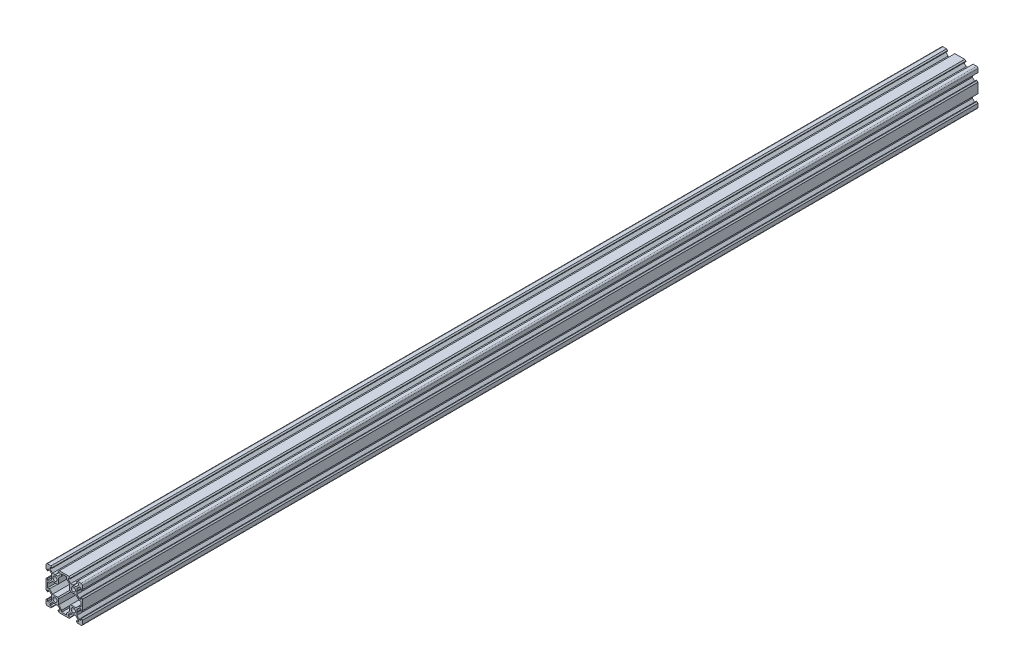
SolidWorks part; units mm, degrees
material "6061-T6 (SS)"
ref_plane "Front Plane" through (0, 0, 0) normal (0, 0, 1) x (1, 0, 0)
ref_plane "Top Plane" through (0, 0, 0) normal (0, 1, 0) x (1, 0, 0)
ref_plane "Right Plane" through (0, 0, 0) normal (1, 0, 0) x (0, 0, -1)
sketch "Sketch1" plane through (0, 0, 0) normal (0, 0, 1) x (1, 0, 0)
  line L1 (18.5, -20) -> (-18.5, -20)
  line L2 (20, -18.5) -> (20, 18.5)
  line L3 (18.5, 20) -> (-18.5, 20)
  line L4 (-20, -18.5) -> (-20, 18.5)
  line L5 (20, -20) -> (-20, 20) construction
  line L6 (20, 20) -> (-20, -20) construction
  circle A0 centre (-10, 10) radius 2.3
  circle A1 centre (10, -10) radius 2.3
  circle A2 centre (10, 10) radius 2.3
  circle A3 centre (-10, -10) radius 2.3
  arc A4 (-18.5, -20) -> (-20, -18.5) centre (-18.5, -18.5) cw
  arc A5 (18.5, -20) -> (20, -18.5) centre (18.5, -18.5) ccw
  arc A6 (20, 18.5) -> (18.5, 20) centre (18.5, 18.5) ccw
  arc A7 (-18.5, 20) -> (-20, 18.5) centre (-18.5, 18.5) ccw
  point P0 (0, 0)
  line B0 (-10, 10) -> (-10, 20) construction
  line B1 (-10, 13.69) -> (-10.21, 13.9)
  line B2 (-10.21, 13.9) -> (-12.8393, 13.9)
  line B3 (-12.8393, 13.9) -> (-15.5, 16.5607)
  line B4 (-15.5, 16.5607) -> (-15.5, 18.2)
  line B5 (-15.5, 18.2) -> (-13.395, 18.2)
  line B6 (-13.395, 18.2) -> (-13.395, 18.815)
  line B7 (-13.395, 18.815) -> (-14.58, 20)
  line B8 (-14.58, 20) -> (-5.42, 20)
  line B9 (-10, 10) -> (-15.9132, 15.9132) construction
  line B10 (-6.605, 18.815) -> (-5.42, 20)
  line B11 (-6.605, 18.2) -> (-6.605, 18.815)
  line B12 (-4.5, 18.2) -> (-6.605, 18.2)
  line B13 (-4.5, 16.5607) -> (-4.5, 18.2)
  line B14 (-7.1607, 13.9) -> (-4.5, 16.5607)
  line B15 (-9.79, 13.9) -> (-7.1607, 13.9)
  line B16 (-10, 13.69) -> (-9.79, 13.9)
  line B17 (10, 10) -> (10, 20) construction
  line B18 (10, 13.69) -> (9.79, 13.9)
  line B19 (9.79, 13.9) -> (7.1607, 13.9)
  line B20 (7.1607, 13.9) -> (4.5, 16.5607)
  line B21 (4.5, 16.5607) -> (4.5, 18.2)
  line B22 (4.5, 18.2) -> (6.605, 18.2)
  line B23 (6.605, 18.2) -> (6.605, 18.815)
  line B24 (6.605, 18.815) -> (5.42, 20)
  line B25 (5.42, 20) -> (14.58, 20)
  line B26 (10, 10) -> (4.0868, 15.9132) construction
  line B27 (13.395, 18.815) -> (14.58, 20)
  line B28 (13.395, 18.2) -> (13.395, 18.815)
  line B29 (15.5, 18.2) -> (13.395, 18.2)
  line B30 (15.5, 16.5607) -> (15.5, 18.2)
  line B31 (12.8393, 13.9) -> (15.5, 16.5607)
  line B32 (10.21, 13.9) -> (12.8393, 13.9)
  line B33 (10, 13.69) -> (10.21, 13.9)
  line B34 (-10, 10) -> (-20, 10) construction
  line B35 (-13.69, 10) -> (-13.9, 9.79)
  line B36 (-13.9, 9.79) -> (-13.9, 7.1607)
  line B37 (-13.9, 7.1607) -> (-16.5607, 4.5)
  line B38 (-16.5607, 4.5) -> (-18.2, 4.5)
  line B39 (-18.2, 4.5) -> (-18.2, 6.605)
  line B40 (-18.2, 6.605) -> (-18.815, 6.605)
  line B41 (-18.815, 6.605) -> (-20, 5.42)
  line B42 (-20, 5.42) -> (-20, 14.58)
  line B43 (-10, 10) -> (-15.9132, 4.0868) construction
  line B44 (-18.815, 13.395) -> (-20, 14.58)
  line B45 (-18.2, 13.395) -> (-18.815, 13.395)
  line B46 (-18.2, 15.5) -> (-18.2, 13.395)
  line B47 (-16.5607, 15.5) -> (-18.2, 15.5)
  line B48 (-13.9, 12.8393) -> (-16.5607, 15.5)
  line B49 (-13.9, 10.21) -> (-13.9, 12.8393)
  line B50 (-13.69, 10) -> (-13.9, 10.21)
  line B51 (-10, -10) -> (-20, -10) construction
  line B52 (-13.69, -10) -> (-13.9, -10.21)
  line B53 (-13.9, -10.21) -> (-13.9, -12.8393)
  line B54 (-13.9, -12.8393) -> (-16.5607, -15.5)
  line B55 (-16.5607, -15.5) -> (-18.2, -15.5)
  line B56 (-18.2, -15.5) -> (-18.2, -13.395)
  line B57 (-18.2, -13.395) -> (-18.815, -13.395)
  line B58 (-18.815, -13.395) -> (-20, -14.58)
  line B59 (-20, -14.58) -> (-20, -5.42)
  line B60 (-10, -10) -> (-15.9132, -15.9132) construction
  line B61 (-18.815, -6.605) -> (-20, -5.42)
  line B62 (-18.2, -6.605) -> (-18.815, -6.605)
  line B63 (-18.2, -4.5) -> (-18.2, -6.605)
  line B64 (-16.5607, -4.5) -> (-18.2, -4.5)
  line B65 (-13.9, -7.1607) -> (-16.5607, -4.5)
  line B66 (-13.9, -9.79) -> (-13.9, -7.1607)
  line B67 (-13.69, -10) -> (-13.9, -9.79)
  line B68 (-10, -10) -> (-10, -20) construction
  line B69 (-10, -13.69) -> (-9.79, -13.9)
  line B70 (-9.79, -13.9) -> (-7.1607, -13.9)
  line B71 (-7.1607, -13.9) -> (-4.5, -16.5607)
  line B72 (-4.5, -16.5607) -> (-4.5, -18.2)
  line B73 (-4.5, -18.2) -> (-6.605, -18.2)
  line B74 (-6.605, -18.2) -> (-6.605, -18.815)
  line B75 (-6.605, -18.815) -> (-5.42, -20)
  line B76 (-5.42, -20) -> (-14.58, -20)
  line B77 (-10, -10) -> (-4.0868, -15.9132) construction
  line B78 (-13.395, -18.815) -> (-14.58, -20)
  line B79 (-13.395, -18.2) -> (-13.395, -18.815)
  line B80 (-15.5, -18.2) -> (-13.395, -18.2)
  line B81 (-15.5, -16.5607) -> (-15.5, -18.2)
  line B82 (-12.8393, -13.9) -> (-15.5, -16.5607)
  line B83 (-10.21, -13.9) -> (-12.8393, -13.9)
  line B84 (-10, -13.69) -> (-10.21, -13.9)
  line B85 (10, -10) -> (10, -20) construction
  line B86 (10, -13.69) -> (10.21, -13.9)
  line B87 (10.21, -13.9) -> (12.8393, -13.9)
  line B88 (12.8393, -13.9) -> (15.5, -16.5607)
  line B89 (15.5, -16.5607) -> (15.5, -18.2)
  line B90 (15.5, -18.2) -> (13.395, -18.2)
  line B91 (13.395, -18.2) -> (13.395, -18.815)
  line B92 (13.395, -18.815) -> (14.58, -20)
  line B93 (14.58, -20) -> (5.42, -20)
  line B94 (10, -10) -> (15.9132, -15.9132) construction
  line B95 (6.605, -18.815) -> (5.42, -20)
  line B96 (6.605, -18.2) -> (6.605, -18.815)
  line B97 (4.5, -18.2) -> (6.605, -18.2)
  line B98 (4.5, -16.5607) -> (4.5, -18.2)
  line B99 (7.1607, -13.9) -> (4.5, -16.5607)
  line B100 (9.79, -13.9) -> (7.1607, -13.9)
  line B101 (10, -13.69) -> (9.79, -13.9)
  line B102 (10, 10) -> (20, 10) construction
  line B103 (13.69, 10) -> (13.9, 10.21)
  line B104 (13.9, 10.21) -> (13.9, 12.8393)
  line B105 (13.9, 12.8393) -> (16.5607, 15.5)
  line B106 (16.5607, 15.5) -> (18.2, 15.5)
  line B107 (18.2, 15.5) -> (18.2, 13.395)
  line B108 (18.2, 13.395) -> (18.815, 13.395)
  line B109 (18.815, 13.395) -> (20, 14.58)
  line B110 (20, 14.58) -> (20, 5.42)
  line B111 (10, 10) -> (15.9132, 15.9132) construction
  line B112 (18.815, 6.605) -> (20, 5.42)
  line B113 (18.2, 6.605) -> (18.815, 6.605)
  line B114 (18.2, 4.5) -> (18.2, 6.605)
  line B115 (16.5607, 4.5) -> (18.2, 4.5)
  line B116 (13.9, 7.1607) -> (16.5607, 4.5)
  line B117 (13.9, 9.79) -> (13.9, 7.1607)
  line B118 (13.69, 10) -> (13.9, 9.79)
  line B119 (10, -10) -> (20, -10) construction
  line B120 (13.69, -10) -> (13.9, -9.79)
  line B121 (13.9, -9.79) -> (13.9, -7.1607)
  line B122 (13.9, -7.1607) -> (16.5607, -4.5)
  line B123 (16.5607, -4.5) -> (18.2, -4.5)
  line B124 (18.2, -4.5) -> (18.2, -6.605)
  line B125 (18.2, -6.605) -> (18.815, -6.605)
  line B126 (18.815, -6.605) -> (20, -5.42)
  line B127 (20, -5.42) -> (20, -14.58)
  line B128 (10, -10) -> (15.9132, -4.0868) construction
  line B129 (18.815, -13.395) -> (20, -14.58)
  line B130 (18.2, -13.395) -> (18.815, -13.395)
  line B131 (18.2, -15.5) -> (18.2, -13.395)
  line B132 (16.5607, -15.5) -> (18.2, -15.5)
  line B133 (13.9, -12.8393) -> (16.5607, -15.5)
  line B134 (13.9, -10.21) -> (13.9, -12.8393)
  line B135 (13.69, -10) -> (13.9, -10.21)
  line B136 (-18.2, -2.7) -> (-18.2, 2.7)
  line B137 (-18.2, 2.7) -> (-16.2393, 2.7)
  line B138 (-16.2393, 2.7) -> (-12.8393, 6.1)
  line B139 (-12.8393, 6.1) -> (-7.1607, 6.1)
  line B140 (-10, 6.1) -> (-10, 0) construction
  line B141 (-10, 0) -> (-18.2, 0) construction
  line B142 (-12.8393, -6.1) -> (-7.1607, -6.1)
  line B143 (-16.2393, -2.7) -> (-12.8393, -6.1)
  line B144 (-18.2, -2.7) -> (-16.2393, -2.7)
  line B145 (-10, 6.1) -> (-10, 10) construction
  line B146 (-10, 10) -> (-15.0927, 4.9073) construction
  line B147 (-10, 10) -> (-6.3747, 6.3747) construction
  line B148 (2.7, 18.2) -> (2.7, 16.2393)
  line B149 (2.7, 16.2393) -> (6.1, 12.8393)
  line B150 (6.1, 12.8393) -> (6.1, 7.1607)
  line B151 (-6.1, 12.8393) -> (-6.1, 7.1607)
  line B152 (-2.7, 16.2393) -> (-6.1, 12.8393)
  line B153 (-2.7, 18.2) -> (-2.7, 16.2393)
  line B154 (2.7, 18.2) -> (-2.7, 18.2)
  line B155 (2.7, -18.2) -> (-2.7, -18.2)
  line B156 (-2.7, -18.2) -> (-2.7, -16.2393)
  line B157 (-2.7, -16.2393) -> (-6.1, -12.8393)
  line B158 (-6.1, -12.8393) -> (-6.1, -7.1607)
  line B159 (6.1, -12.8393) -> (6.1, -7.1607)
  line B160 (2.7, -16.2393) -> (6.1, -12.8393)
  line B161 (2.7, -18.2) -> (2.7, -16.2393)
  line B162 (0, 18.2) -> (0, -18.2) construction
  line B163 (12.8393, -6.1) -> (7.1607, -6.1)
  line B164 (16.2393, -2.7) -> (12.8393, -6.1)
  line B165 (18.2, -2.7) -> (16.2393, -2.7)
  line B166 (18.2, -2.7) -> (18.2, 2.7)
  line B167 (18.2, 2.7) -> (16.2393, 2.7)
  line B168 (16.2393, 2.7) -> (12.8393, 6.1)
  line B169 (12.8393, 6.1) -> (7.1607, 6.1)
  line B170 (-7.1607, 6.1) -> (-6.1, 7.1607)
  line B171 (6.1, 7.1607) -> (7.1607, 6.1)
  line B172 (7.1607, -6.1) -> (6.1, -7.1607)
  line B173 (-6.1, -7.1607) -> (-7.1607, -6.1)
  dimension "D4" = 4.6
  dimension "D5" = 1.5
  dimension "D1" = 40
  dimension "D2" = 10
  dimension "D3" = 10
sketch_block_instance "V Slot 2-1"
sketch_block "V Slot 2" parameters "D1"=10, "D2"=11, "D3"=4.3, "D4"=1.8, "D5"=0.21, "D6"=45, "D7"=9.16, "D8"=1.5, "D9"=6.79
sketch_block_instance "V Slot 2-2"
sketch_block_instance "V Slot 2-3"
sketch_block_instance "V Slot 2-4"
sketch_block_instance "V Slot 2-5"
sketch_block_instance "V Slot 2-6"
sketch_block_instance "V Slot 2-7"
sketch_block_instance "V Slot 2-8"
sketch_block_instance "Center Cutout 2-1"
sketch_block "Center Cutout 2" parameters "D1"=5.4, "D2"=12.2, "D3"=8.2, "D4"=45, "D5"=10, "D6"=1.5
extrude "Boss-Extrude1" add sketch "Sketch1" along normal blind 984.25 contours B135 B120 B121 B122 B123 B124 B125 B126 L2 B112 B113 B114 B115 B116 B117 B118 B103 B104 B105 B106 B107 B108 B109 A6 L3 B27 B28 B29 B30 B31 B32 B33 B18 B19 B20 B21 B22 B23 B24 B10 B11 B12 B13 B14 B15 B16 B1 B2 B3
